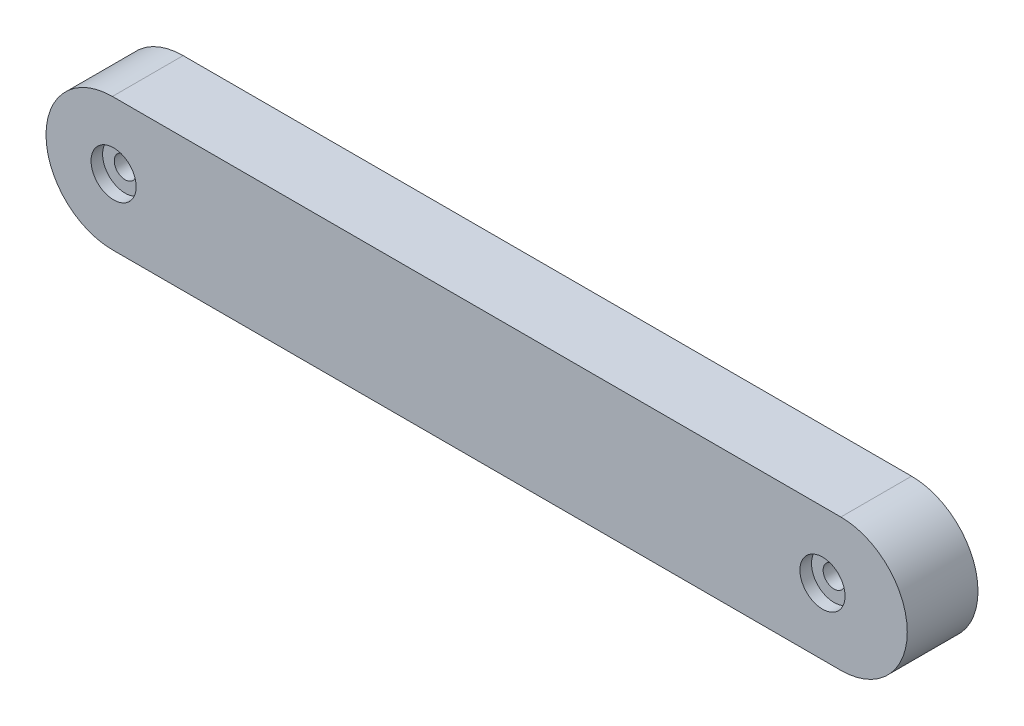
SolidWorks part; units mm, degrees
other "Markup1"
sketch "Sketch6" plane through (-118.7894, -9.9264, 10.5687) normal (0, 0, 1) x (1, 0, 0)
other "DetailItem1"
other "DetailItem2"
ref_plane "Front Plane" through (0, 0, 0) normal (0, 0, 1) x (1, 0, 0)
ref_plane "Top Plane" through (0, 0, 0) normal (0, 1, 0) x (1, 0, 0)
ref_plane "Right Plane" through (0, 0, 0) normal (1, 0, 0) x (0, 0, -1)
sketch "Sketch1" plane through (0, 0, 0) normal (0, 0, 1) x (1, 0, 0)
  line L0 (0, 0) -> (-108.863, 0) construction
  line L1 (0, -9.9264) -> (-108.863, -9.9264)
  line L2 (0, 9.9264) -> (-108.863, 9.9264)
  arc A0 (0, -9.9264) -> (0, 9.9264) centre (0, 0) ccw
  arc A1 (-108.863, 9.9264) -> (-108.863, -9.9264) centre (-108.863, 0) ccw
  point P3 (-54.4315, 0)
  dimension "D2" = 9.9264
  dimension "D1" = 108.863
extrude "Boss-Extrude1" add sketch "Sketch1" along normal blind 10.5687
hole_wizard "CBORE for #4 Binding Head Machine Screw1" positions "Sketch2" profile "Sketch3" counterbore size "#4" standard "ANSI Inch" end condition through all
sketch "Sketch2" plane through (0, 0, 10.5687) normal (0, 0, 1) x (1, 0, 0)
  point P0 (-2.7443, 0)
sketch "Sketch3" plane through (-2.7443, 0, 10.5687) normal (1, 0, 0) x (0, -1, 0)
  line L0 (0, 0) -> (0, 10.5687)
  line L1 (0, 10.5687) -> (1.6319, 10.5687)
  line L3 (1.6319, 10.5687) -> (1.632, 1.7272)
  line L4 (1.632, 1.7272) -> (3.3731, 1.7272)
  line L5 (3.3731, 1.7272) -> (3.3731, 0)
  line L7 (3.3731, 0) -> (0, 0)
  line L11 (0, -6.35) -> (0, 107.95) construction
  dimension "Thru Hole Dia." = 3.2639
  dimension "Thru Hole Depth" = 10.5687
  dimension "C'Bore Dia." = 6.7462
  dimension "C'Bore Depth" = 1.7272
hole_wizard "CBORE for #4 Binding Head Machine Screw2" positions "Sketch4" profile "Sketch5" counterbore size "#4" standard "ANSI Inch" end condition through all
sketch "Sketch4" plane through (0, 0, 10.5687) normal (0, 0, 1) x (1, 0, 0)
  point P0 (-108.688, 0)
sketch "Sketch5" plane through (-108.688, 0, 10.5687) normal (1, 0, 0) x (0, -1, 0)
  line L0 (0, 0) -> (0, 10.5687)
  line L1 (0, 10.5687) -> (1.6319, 10.5687)
  line L3 (1.6319, 10.5687) -> (1.632, 1.7272)
  line L4 (1.632, 1.7272) -> (3.3731, 1.7272)
  line L5 (3.3731, 1.7272) -> (3.3731, 0)
  line L7 (3.3731, 0) -> (0, 0)
  line L11 (0, -6.35) -> (0, 107.95) construction
  dimension "Thru Hole Dia." = 3.2639
  dimension "Thru Hole Depth" = 10.5687
  dimension "C'Bore Dia." = 6.7462
  dimension "C'Bore Depth" = 1.7272
